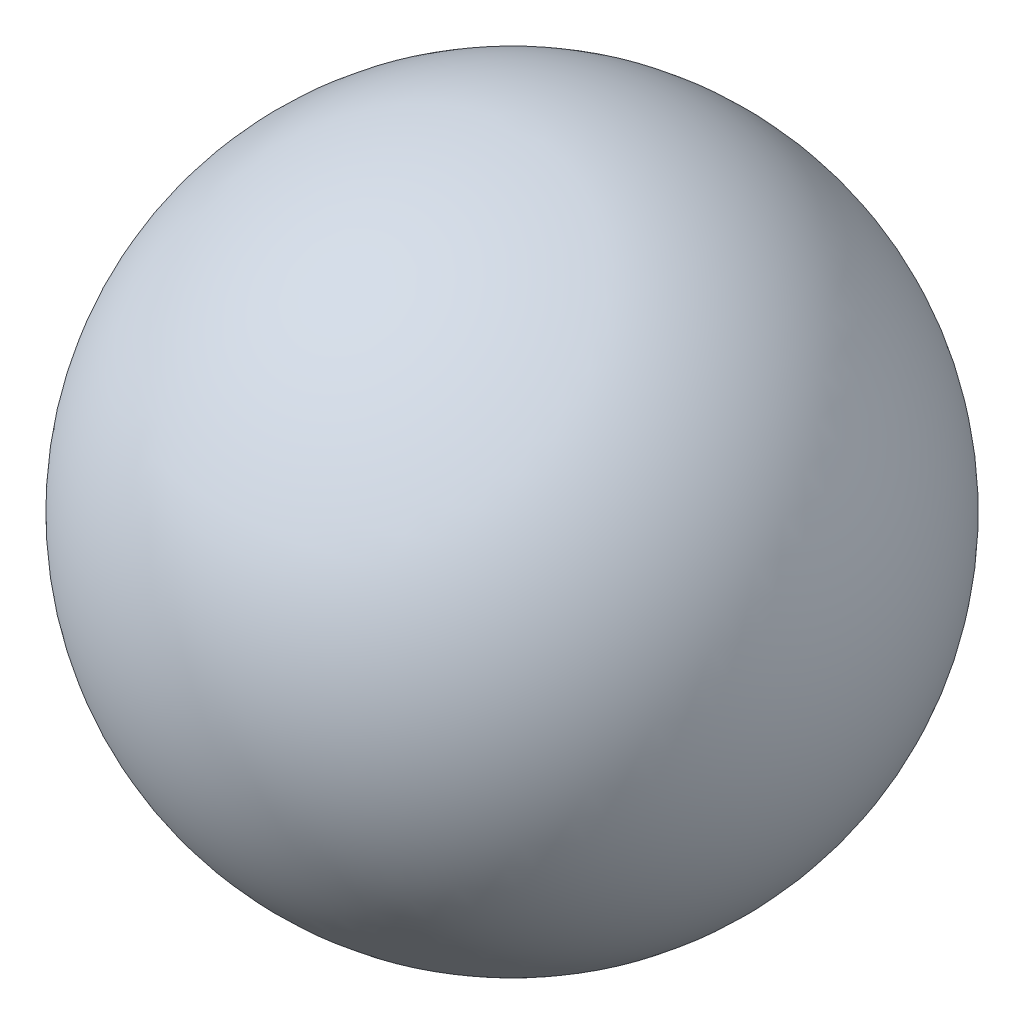
SolidWorks part; units mm, degrees
material "Chrome Stainless Steel"
ref_plane "Front Plane" through (0, 0, 0) normal (0, 0, 1) x (1, 0, 0)
ref_plane "Top Plane" through (0, 0, 0) normal (0, 1, 0) x (1, 0, 0)
ref_plane "Right Plane" through (0, 0, 0) normal (1, 0, 0) x (0, 0, -1)
sketch "Sketch1" plane through (0, 0, 0) normal (0, 0, 1) x (1, 0, 0)
  line L0 (0, 6.35) -> (0, -6.35)
  arc A0 (0, 6.35) -> (0, -6.35) centre (0, 0) ccw
  dimension "D1" = 12.7
revolve "Revolve1" add sketch "Sketch1" angle 360 about L0
